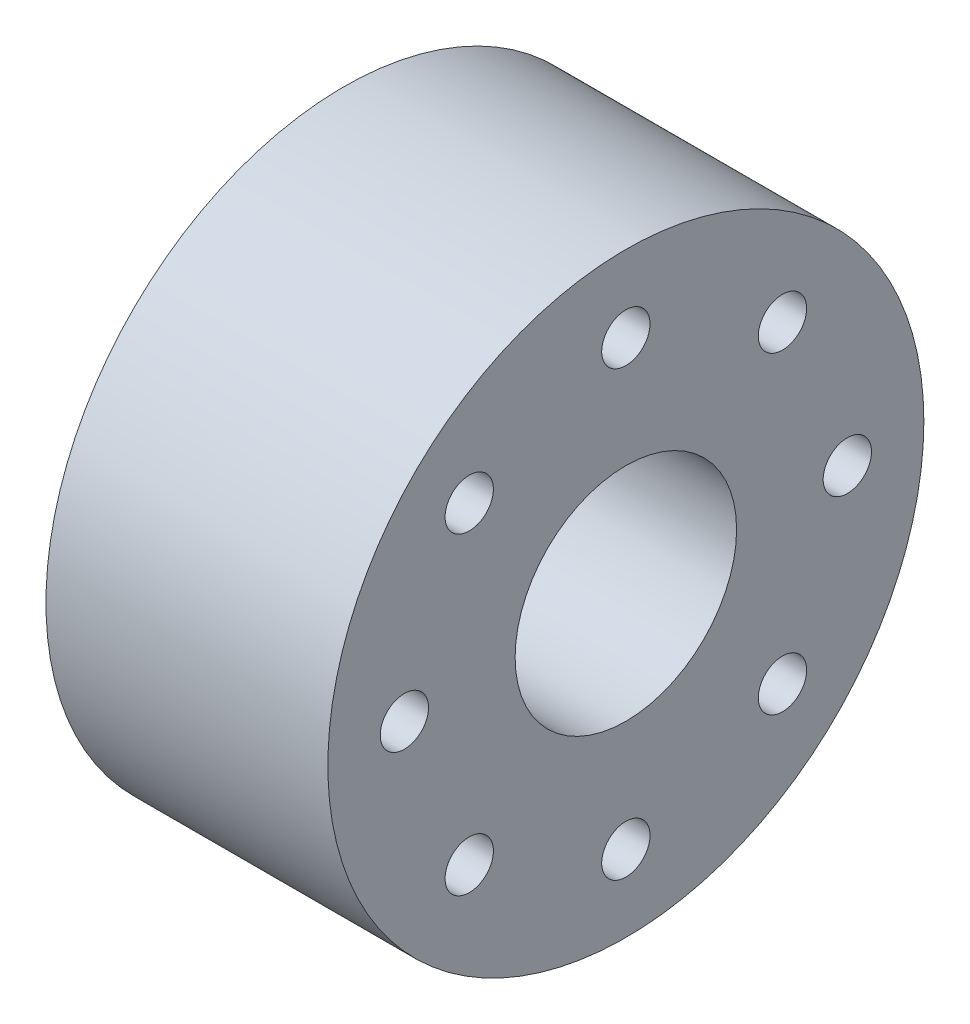
SolidWorks part; units mm, degrees
material "Alumina"
ref_plane "Front Plane" through (0, 0, 0) normal (0, 0, 1) x (1, 0, 0)
ref_plane "Top Plane" through (0, 0, 0) normal (0, 1, 0) x (1, 0, 0)
ref_plane "Right Plane" through (0, 0, 0) normal (1, 0, 0) x (0, 0, -1)
sketch "Sketch1" plane through (0, 0, 0) normal (1, 0, 0) x (0, 0, -1)
  circle A0 centre (0, 0) radius 14.8
  dimension "D1" = 29.6
extrude "Boss-Extrude1" add sketch "Sketch1" along normal blind 14
sketch "Sketch2" plane through (14, 0, 0) normal (1, 0, 0) x (0, 0, -1)
  circle A0 centre (0, 0) radius 11 construction
  circle A1 centre (0, 11) radius 1.2
  circle A2 centre (7.7782, 7.7782) radius 1.2
  circle A3 centre (11, 0) radius 1.2
  circle A4 centre (7.7782, -7.7782) radius 1.2
  circle A5 centre (0, 0) radius 14.8 construction
  circle A6 centre (0, -11) radius 1.2
  circle A7 centre (-7.7782, -7.7782) radius 1.2
  circle A8 centre (-11, 0) radius 1.2
  circle A9 centre (-7.7782, 7.7782) radius 1.2
  point P14 (0, 0)
  dimension "D1" = 22
  dimension "D2" = 2.4
  dimension "D3" = 8
extrude "Cut-Extrude1" cut sketch "Sketch2" against normal through all both and the other way through all
sketch "Sketch3" plane through (0, 0, 0) normal (-1, 0, 0) x (0, 0, 1)
  circle A0 centre (0, 0) radius 5.5
  dimension "D1" = 11
extrude "Cut-Extrude2" cut sketch "Sketch3" against normal up to surface (14 mm away) up to face at (14, 11, -1.2)
sketch "Sketch5" plane through (14, 0, 0) normal (1, 0, 0) x (0, 0, -1)
  circle A0 centre (7.7782, 7.7782) radius 2.5
  circle A1 centre (-7.7782, -7.7782) radius 2.5
  circle A2 centre (7.7782, -7.7782) radius 2.5
  circle A3 centre (-7.7782, 7.7782) radius 2.5
  dimension "D1" = 5
extrude "Cut-Extrude3" cut sketch "Sketch5" against normal through all from offset 9
